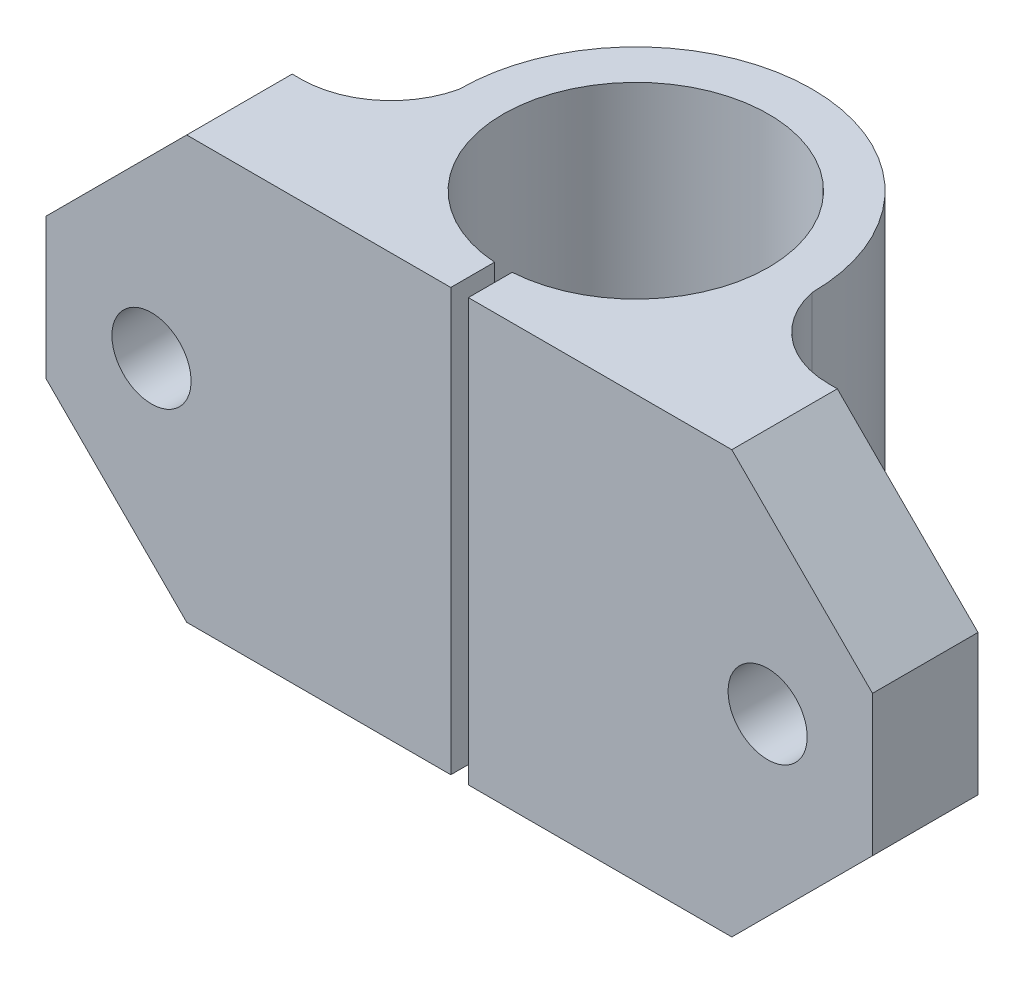
SolidWorks part; units mm, degrees
ref_plane "Front Plane" through (0, 0, 0) normal (0, 0, 1) x (1, 0, 0)
ref_plane "Top Plane" through (0, 0, 0) normal (0, 1, 0) x (1, 0, 0)
ref_plane "Right Plane" through (0, 0, 0) normal (1, 0, 0) x (0, 0, -1)
ref_plane "Plane1" through (0, 24, 0) normal (0, 1, 0) x (1, 0, 0)
sketch "Sketch1" plane through (0, 24, 0) normal (0, 1, 0) x (1, 0, 0)
  line L0 (0, 0) -> (47, 0)
  line L1 (47, 0) -> (47, 6)
  line L2 (47, 6) -> (38.5, 6)
  line L3 (8.5, 6) -> (0, 6)
  line L4 (0, 6) -> (0, 0)
  arc A0 (38.5, 6) -> (33.5414, 10.0218) centre (38.5, 11.0678) cw
  arc A1 (33.5414, 10.0218) -> (13.4959, 9.9961) centre (23.5186, 10.0227) ccw
  arc A2 (13.4959, 9.9961) -> (8.5, 6) centre (8.5, 11.121) cw
extrude "Boss-Extrude1" add sketch "Sketch1" against normal blind 24
sketch "Sketch2" plane through (0, 0, 0) normal (0, -1, 0) x (1, 0, 0)
  line L0 (24.0186, 0) -> (23.0186, 0)
  line L1 (23.0186, 0) -> (23.0186, -2.4893)
  line L2 (24.0186, -2.4893) -> (24.0186, 0)
  arc A0 (23.0186, -2.4893) -> (24.0186, -2.4893) centre (23.5186, -10.0227) cw
extrude "Cut-Extrude1" cut sketch "Sketch2" against normal through all
ref_plane "Plane2" through (0, 0, -10.0227) normal (0, 0, -1) x (-1, 0, 0)
sketch "Sketch3" plane through (0, 0, -10.0227) normal (0, 0, -1) x (-1, 0, 0)
  line L0 (-31.0686, 0) -> (-23.5186, 0)
  line L1 (-23.5186, 0) -> (-23.5186, 24)
  line L2 (-23.5186, 24) -> (-31.0686, 24)
  line L3 (-31.0686, 24) -> (-31.0686, 0)
  line L4 (-23.5186, 0) -> (-23.5186, 24) construction
revolve "Cut-Revolve1" cut sketch "Sketch3" angle 360 about L4
hole_wizard "Ø4.5 (4.5) Diameter Hole1" positions "Sketch5" profile "Sketch4" hole size "Ø4.5" standard "ANSI Metric"
sketch "Sketch5" plane through (0, 0, -6) normal (0, 0, -1) x (-1, 0, 0)
  point P0 (-41.0373, 12)
  point P1 (-6, 12)
sketch "Sketch4" plane through (41.0373, 12, -6) normal (1, 0, 0) x (0, 1, 0)
  line L0 (0, 0) -> (0, 6)
  line L1 (0, 6) -> (2.25, 6)
  line L2 (2.25, 6) -> (2.25, 0)
  line L5 (2.25, 0) -> (0, 0)
  line L11 (0, -6.35) -> (0, 107.95) construction
  dimension "Thru Hole Dia." = 4.5
  dimension "Thru Hole Depth" = 6
chamfer "Chamfer1" distance 8 angle 45 4 edges at (0, 0, -3) (47, 0, -3) (0, 24, -3) (47, 24, -3)
